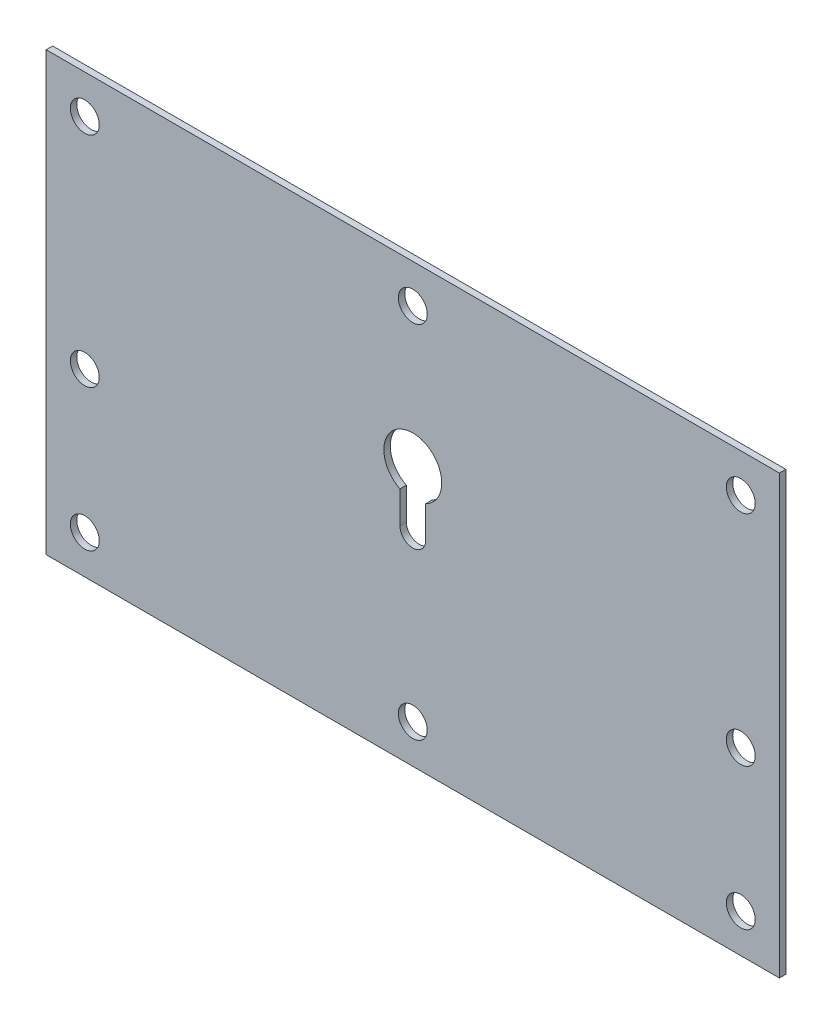
SolidWorks part; units mm, degrees
ref_plane "Спереди" through (0, 0, 0) normal (0, 0, 1) x (1, 0, 0)
ref_plane "Сверху" through (0, 0, 0) normal (0, 1, 0) x (1, 0, 0)
ref_plane "Справа" through (0, 0, 0) normal (1, 0, 0) x (0, 0, -1)
sketch "Эскиз1" plane through (0, 0, 0) normal (0, 0, 1) x (1, 0, 0)
  line L1 (0, 0) -> (114, 0)
  line L2 (0, 0) -> (0, 68)
  line L3 (0, 68) -> (114, 68)
  line L4 (114, 0) -> (114, 68)
  dimension "D1" = 114
  dimension "D2" = 68
extrude "Бобышка-Вытянуть1" add sketch "Эскиз1" along normal blind 1
sketch "Эскиз2" plane through (0, 0, 1) normal (0, 0, 1) x (1, 0, 0)
  line L0 (6, 62) -> (6, 6) construction
  line L1 (6, 6) -> (108, 6) construction
  line L2 (108, 6) -> (108, 62) construction
  line L3 (108, 62) -> (6, 62) construction
  line L4 (6, 28) -> (108, 28) construction
  line L5 (0, 68) -> (0, 0) construction
  line L6 (57, 62) -> (57, 6) construction
  line L7 (114, 0) -> (114, 68) construction
  line L8 (0, 0) -> (114, 0) construction
  line L9 (114, 68) -> (0, 68) construction
  line L10 (57, 40.4) -> (57, 31.4) construction
  line L11 (59, 36.3689) -> (59, 31.4)
  line L12 (55, 36.3689) -> (55, 31.4)
  circle A0 centre (6, 62) radius 2.25
  circle A1 centre (6, 28) radius 2.25
  circle A2 centre (6, 6) radius 2.25
  circle A3 centre (57, 6) radius 2.25
  circle A4 centre (57, 62) radius 2.25
  circle A5 centre (108, 62) radius 2.25
  circle A6 centre (108, 28) radius 2.25
  circle A7 centre (108, 6) radius 2.25
  arc A8 (59, 36.3689) -> (55, 36.3689) centre (57, 40.4) ccw
  arc A10 (55, 31.4) -> (59, 31.4) centre (57, 31.4) ccw
  point P26 (57, 35.9)
  point P28 (0, 0)
  point P30 (59, 36.3689)
  point P32 (0, 0)
  point P34 (0, 0)
  point P35 (55, 31.4)
  dimension "D6" = 4.5
  dimension "D7" = 9
  dimension "D8" = 2
  dimension "D10" = 27.6
  dimension "D1" = 6
  dimension "D2" = 6
  dimension "D3" = 6
  dimension "D4" = 22
  dimension "D5" = 6
  dimension "D9" = 9
  dimension "D11" = 2
  dimension "D12" = 2
extrude "Вырез-Вытянуть1" cut sketch "Эскиз2" against normal up to next
